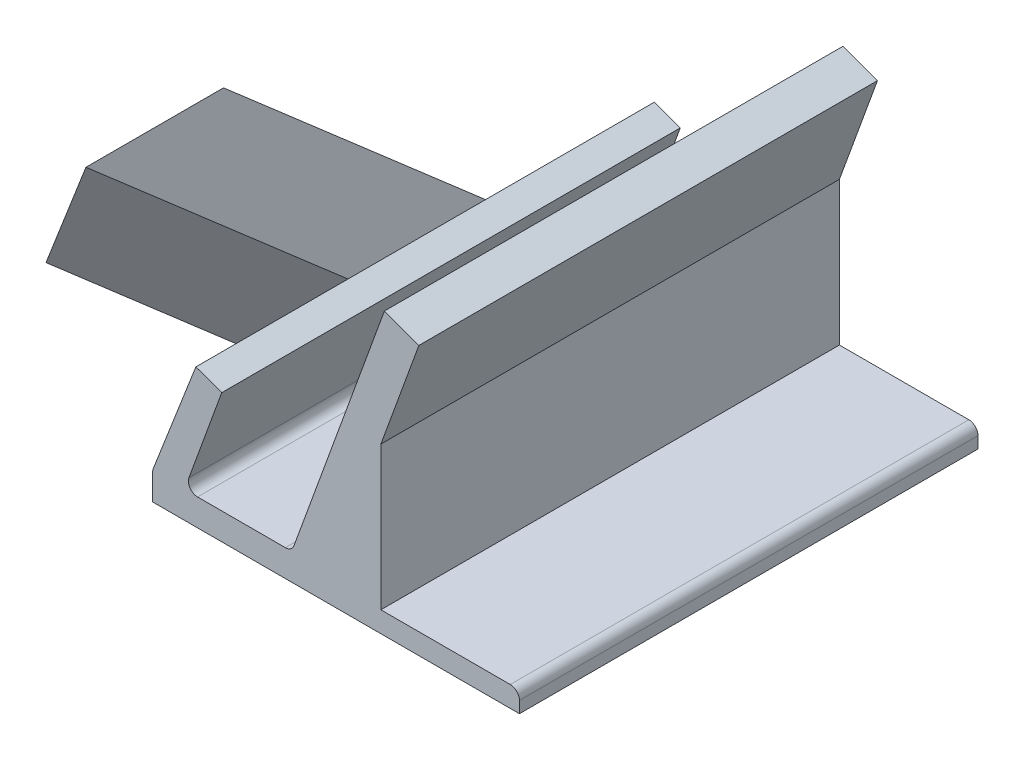
SolidWorks part; units mm, degrees
ref_plane "Alzado" through (0, 0, 0) normal (0, 0, 1) x (1, 0, 0)
ref_plane "Planta" through (0, 0, 0) normal (0, 1, 0) x (1, 0, 0)
ref_plane "Vista lateral" through (0, 0, 0) normal (1, 0, 0) x (0, 0, -1)
sketch "Croquis1" plane through (0, 0, 0) normal (0, 0, 1) x (1, 0, 0)
  line L0 (-84.4925, -6.9218) -> (-44.4925, -6.9218)
  line L1 (-44.4925, -6.9218) -> (-44.4925, -5.6609)
  line L2 (-84.4925, -6.9218) -> (-84.4925, -4.1096)
  line L3 (-84.4243, -3.7467) -> (-80.1293, 7.2806)
  line L4 (-84.4925, -3.9218) -> (-84.4746, -3.1189) construction
  line L6 (-77.2974, 6.2261) -> (-80.5307, -2.6574)
  line L7 (-79.591, -3.9994) -> (-70.0134, -3.9994)
  line L8 (-69.0737, -3.3414) -> (-59.5565, 22.8069)
  line L10 (-69.3132, -3.9994) -> (-69.3132, 2.3689) construction
  line L11 (-59.5565, 22.8069) -> (-59.2145, 23.7466)
  line L12 (-45.4925, -4.6609) -> (-59.6021, -4.6609)
  line L13 (-59.6021, -4.6609) -> (-59.6021, 10.9864)
  line L14 (-59.6021, 10.9864) -> (-55.7977, 21.4388)
  line L15 (-59.2145, 23.7466) -> (-55.4557, 22.3785)
  line L16 (-55.4557, 22.3785) -> (-55.7977, 21.4388)
  line L17 (-77.2974, 6.2261) -> (-76.9554, 7.1658)
  line L18 (-76.9554, 7.1658) -> (-79.7744, 8.1919)
  line L19 (-79.7744, 8.1919) -> (-80.1293, 7.2806)
  arc A0 (-44.4925, -5.6609) -> (-45.4925, -4.6609) centre (-45.4925, -5.6609) ccw
  arc A1 (-84.4925, -4.1096) -> (-84.4243, -3.7467) centre (-83.4925, -4.1096) cw
  arc A2 (-80.5307, -2.6574) -> (-79.591, -3.9994) centre (-79.591, -2.9994) ccw
  arc A3 (-70.0134, -3.9994) -> (-69.0737, -3.3414) centre (-70.0134, -2.9994) ccw
  point P32 (-79.7744, 8.1919)
  dimension "D5" = 1
  dimension "D1" = 20
  dimension "D2" = 13
  dimension "D3" = 11
  dimension "D4" = 20
extrude "Saliente-Extruir1" add sketch "Croquis1" along normal blind 50
sketch "Croquis3" plane through (-72.037, 28.0575, 0) normal (-0.9318, 0.3629, 0) x (0, 0, 1)
  line L6 (25, -28.2143) -> (25, -34.2143)
  line L7 (17.5, -22.2143) -> (32.5, -22.2143)
  line L8 (17.5, -22.2143) -> (17.5, -34.2143)
  line L9 (17.5, -34.2143) -> (32.5, -34.2143)
  line L10 (32.5, -22.2143) -> (32.5, -34.2143)
  line L11 (17.5, -22.2143) -> (32.5, -34.2143) construction
  line L12 (17.5, -34.2143) -> (32.5, -22.2143) construction
  circle A0 centre (25, -28.2143) radius 5
  point P9 (25, -28.2143)
  dimension "D1" = 15
  dimension "D2" = 12
ref_plane "Plano1" through (-12.4174, -31.8815, 0) normal (-0.3629, -0.9318, 0) x (0, 0, 1)
sketch "Croquis5" plane through (-12.4174, -31.8815, 0) normal (-0.3629, -0.9318, 0) x (0, 0, 1)
  line L0 (17.5, 77.3082) -> (32.2224, 85.8082)
  line L1 (17.5, 77.3082) -> (32.5, 77.3082)
  line L2 (32.5, 77.3082) -> (47.2224, 85.8082)
  line L3 (47.2224, 85.8082) -> (32.2224, 85.8082)
  line L4 (25, 77.3082) -> (39.7224, 85.8082)
  dimension "D1" = 30
  dimension "D2" = 17
ref_plane "Plano2" through (-43.9405, 17.1143, -27.2254) normal (0.807, -0.3143, 0.5) x (0.4659, -0.1815, -0.866)
sketch "Croquis7" plane through (-43.9405, 17.1143, -27.2254) normal (0.807, -0.3143, 0.5) x (0.4659, -0.1815, -0.866)
  line L0 (-60.3047, -28.2143) -> (-104.6077, -2.636) construction
  line L1 (-60.3047, -28.2143) -> (-86.2855, -13.2143)
ref_plane "Plano3" through (-88.9375, 20.4588, 47.5) normal (-0.222, 0.6231, 0.75) x (0.975, 0.1419, 0.1708)
sweep "Barrer9" add profiles "Croquis3" path "Croquis7"
ref_plane "Plano5" through (-72.349, -25.8926, 0) normal (-0.9415, -0.337, 0) x (0, 0, 1)
